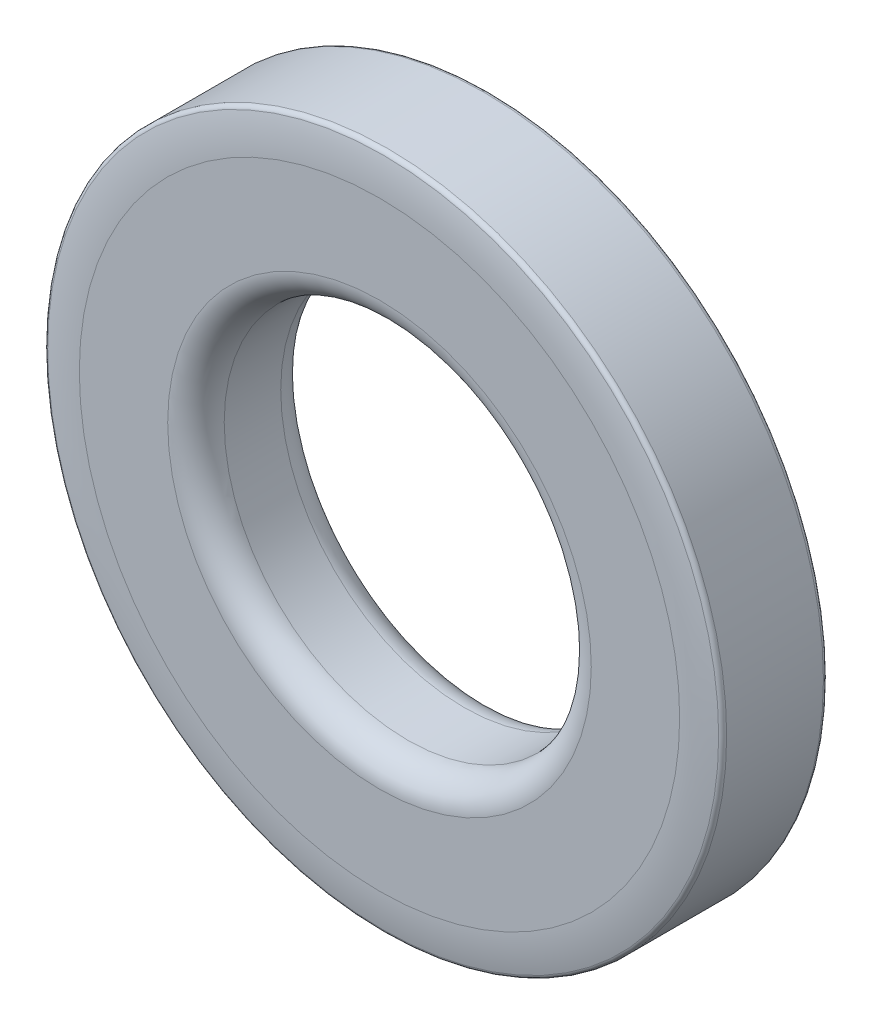
SolidWorks part; units mm, degrees
ref_plane "Front Plane" through (0, 0, 0) normal (0, 0, 1) x (1, 0, 0)
ref_plane "Top Plane" through (0, 0, 0) normal (0, 1, 0) x (1, 0, 0)
ref_plane "Right Plane" through (0, 0, 0) normal (1, 0, 0) x (0, 0, -1)
sketch "Sketch1" plane through (0, 0, 0) normal (0, 0, 1) x (1, 0, 0)
  line L0 (0, 0) -> (0, -5.1562) construction
  line L1 (0, 0) -> (5.1562, 0) construction
  circle A0 centre (0, 0) radius 5.1562
  circle A1 centre (0, 0) radius 9.525
  point P4 (5.1562, 0)
  dimension "OD" = 19.05
  dimension "ID" = 10.3124
  dimension "D1" = 90
sketch "Sketch2" plane through (0, 0, 0) normal (1, 0, 0) x (0, 0, -1)
  line L0 (-1.5875, 0) -> (1.5875, 0)
  line L2 (1.5875, -9.525) -> (-1.5875, -9.525)
  line L3 (1.5875, -9.525) -> (1.5875, 9.525)
  line L4 (1.5875, 9.525) -> (-1.5875, 9.525)
  line L5 (-1.5875, -9.525) -> (-1.5875, 9.525)
  line L6 (1.5875, -9.525) -> (-1.5875, 9.525) construction
  line L7 (1.5875, 9.525) -> (-1.5875, -9.525) construction
  point P0 (0, 0)
  point P3 (0, 0)
  point P11 (0, 9.525)
  dimension "Thickness" = 3.175
sketch "Sketch3" plane through (0, 0, 0) normal (0, 0, 1) x (1, 0, 0)
  circle A0 centre (0, 0) radius 5.1562 construction
  circle A1 centre (0, 0) radius 9.525 construction
  circle A2 centre (0, 0) radius 5.1562
  circle A3 centre (0, 0) radius 9.525
extrude "Boss-Extrude1" add sketch "Sketch3" along normal mid plane 3.175
sketch "Sketch4" plane through (0, 0, 0) normal (1, 0, 0) x (0, 0, -1)
  line L0 (-1.5875, 9.525) -> (-1.5875, -9.525) construction
  line L1 (1.5875, 9.525) -> (-1.5875, 9.525) construction
  line L2 (-1.4605, 9.525) -> (-1.5875, 9.525)
  line L3 (-1.5875, 9.525) -> (-1.5875, 8.4328)
  line L4 (-0.7937, 5.1562) -> (-1.5875, 5.1562)
  line L5 (-1.5875, 5.1562) -> (-1.5875, 5.95)
  arc A0 (-1.5875, 8.4328) -> (-1.4605, 9.525) centre (3.1725, 8.4328) cw
  arc A1 (-1.5875, 5.95) -> (-0.7937, 5.1562) centre (-0.7938, 5.95) ccw
  dimension "D1" = 0.127
  dimension "D2" = 1.0922
  dimension "D3" = 0.7937
revolve "Cut-Revolve1" cut sketch "Sketch4" angle 360 about L0
mirror "Mirror1" about plane through (0, 0, 0) normal (0, 0, 1) of "Cut-Revolve1"
fillet "Fillet1" radius 0.127 2 edges at (0, -9.525, 1.4605) (0, -9.525, -1.4605)
equation "\"D1@Boss-Extrude1\" = \"Thickness@Sketch2\""
equation "\"D2@Sketch4\"=(\"OD@Sketch1\"-\"ID@Sketch1\")*.125"
equation "\"D3@Sketch4\"=\"Thickness@Sketch2\"*.25"
